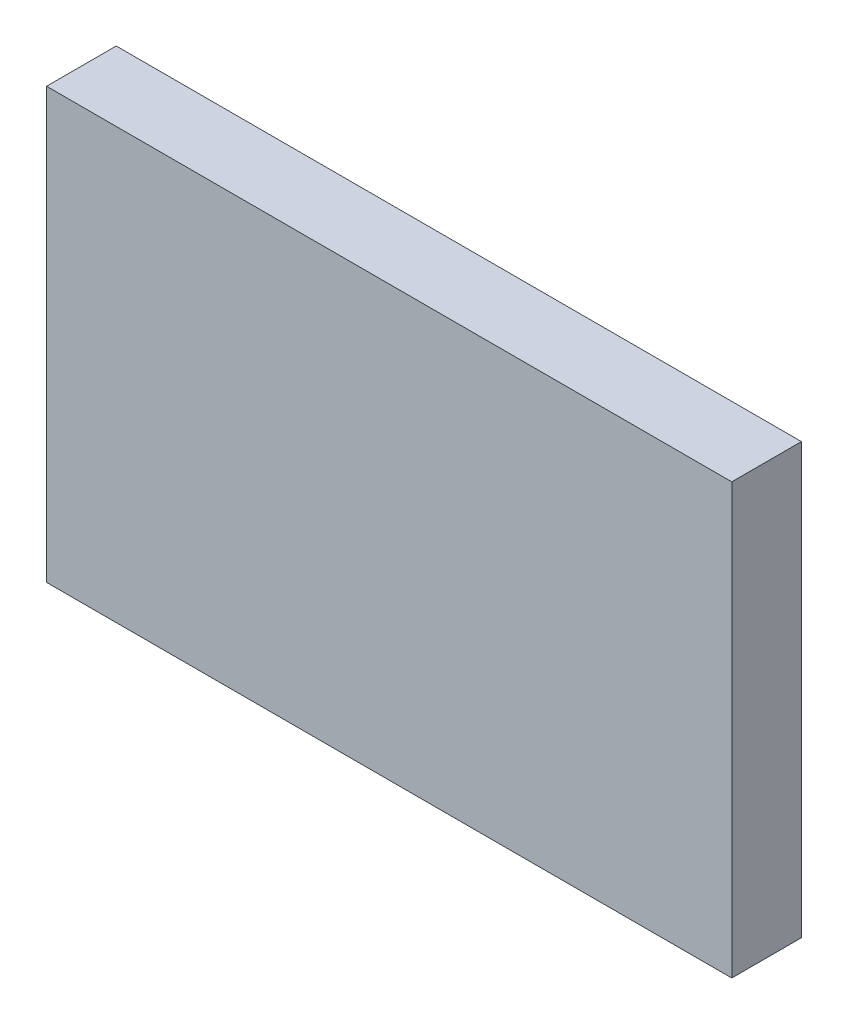
SolidWorks part; units mm, degrees
ref_plane "Front Plane" through (0, 0, 0) normal (0, 0, 1) x (1, 0, 0)
ref_plane "Top Plane" through (0, 0, 0) normal (0, 1, 0) x (1, 0, 0)
ref_plane "Right Plane" through (0, 0, 0) normal (1, 0, 0) x (0, 0, -1)
sketch "Sketch1" plane through (0, 0, 0) normal (0, 0, 1) x (1, 0, 0)
  line L1 (29.5, 18.5) -> (-29.5, 18.5)
  line L2 (29.5, 18.5) -> (29.5, -18.5)
  line L3 (29.5, -18.5) -> (-29.5, -18.5)
  line L4 (-29.5, 18.5) -> (-29.5, -18.5)
  line L5 (0, -18.5) -> (0, 18.5) construction
  line L6 (29.5, 0) -> (-29.5, 0) construction
  point P0 (0, 0)
  dimension "D1" = 59
  dimension "D2" = 37
extrude "Boss-Extrude1" add sketch "Sketch1" along normal blind 6
